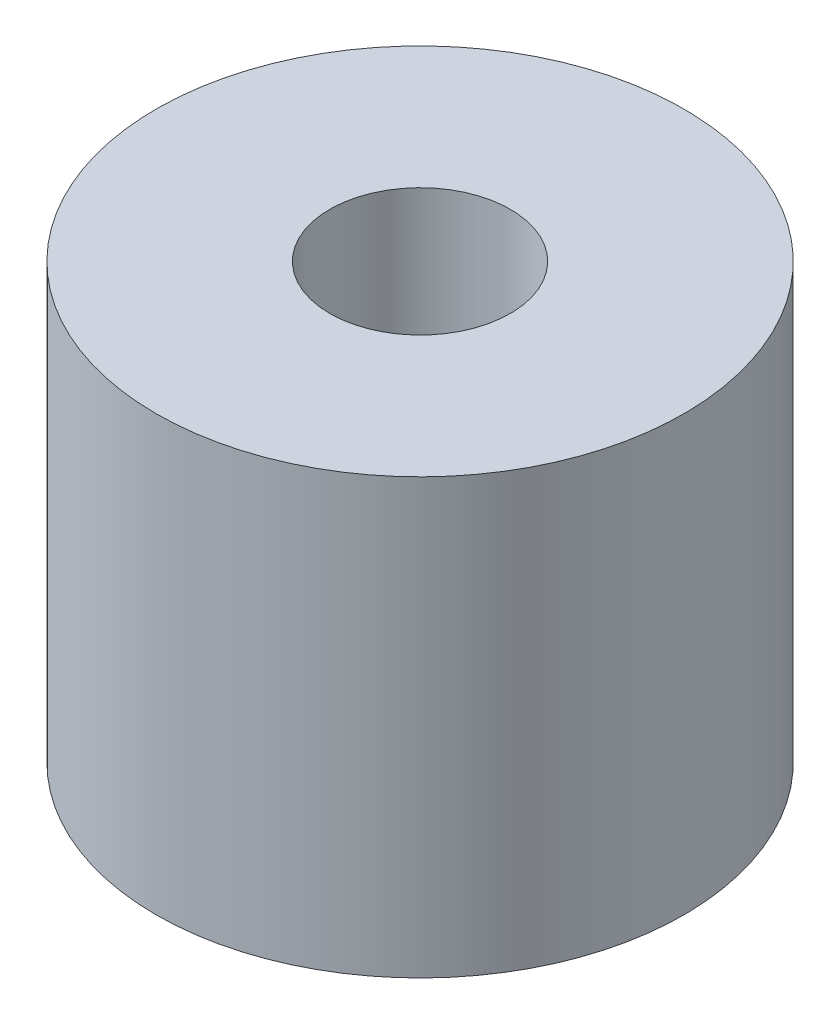
SolidWorks part; units mm, degrees
ref_plane "Front Plane" through (0, 0, 0) normal (0, 0, 1) x (1, 0, 0)
ref_plane "Top Plane" through (0, 0, 0) normal (0, 1, 0) x (1, 0, 0)
ref_plane "Right Plane" through (0, 0, 0) normal (1, 0, 0) x (0, 0, -1)
sketch "Sketch1" plane through (0, 0, 0) normal (0, 1, 0) x (1, 0, 0)
  circle A0 centre (0, 0) radius 7.6
  circle A1 centre (0, 0) radius 2.6
  dimension "D1" = 5.2
  dimension "D2" = 15.2
extrude "Boss-Extrude1" add sketch "Sketch1" along normal blind 12.5
